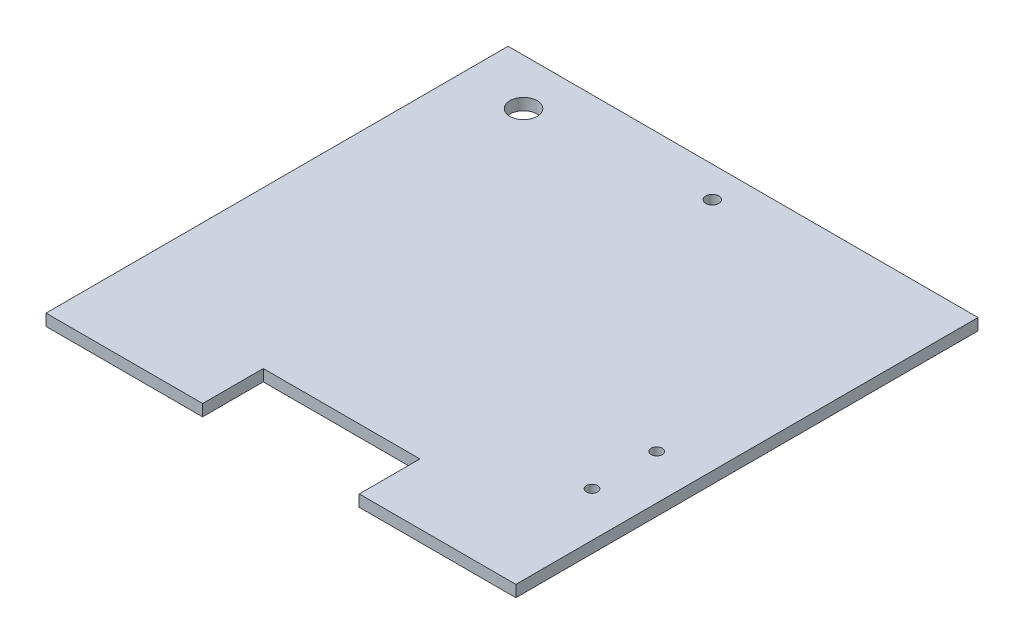
SolidWorks part; units mm, degrees
ref_plane "Front Plane" through (0, 0, 0) normal (0, 0, 1) x (1, 0, 0)
ref_plane "Top Plane" through (0, 0, 0) normal (0, 1, 0) x (1, 0, 0)
ref_plane "Right Plane" through (0, 0, 0) normal (1, 0, 0) x (0, 0, -1)
sketch "Sketch1" plane through (0, 0, 0) normal (0, 1, 0) x (1, 0, 0)
  line L1 (-96.84, -95.25) -> (96.84, -95.25)
  line L2 (-96.84, -95.25) -> (-96.84, 95.25)
  line L3 (-96.84, 95.25) -> (96.84, 95.25)
  line L4 (96.84, -95.25) -> (96.84, 95.25)
  line L5 (-96.84, -95.25) -> (96.84, 95.25) construction
  line L6 (-96.84, 95.25) -> (96.84, -95.25) construction
  point P0 (0, 0)
  dimension "D1" = 193.68
  dimension "D2" = 190.5
extrude "Boss-Extrude1" add sketch "Sketch1" along normal blind 4.78
sketch "Sketch2" plane through (0, 4.78, 0) normal (0, 1, 0) x (1, 0, 0)
  line L0 (96.84, 95.25) -> (-96.84, 95.25) construction
  line L1 (96.84, -95.25) -> (96.84, 95.25) construction
  circle A0 centre (0, 82.55) radius 2.6797
  point P4 (0, 95.25)
  dimension "D1" = 5.3594
  dimension "D2" = 12.7
  dimension "D3" = 96.84
extrude "Cut-Extrude1" cut sketch "Sketch2" against normal through all
sketch "Sketch3" plane through (0, 4.78, 0) normal (0, 1, 0) x (1, 0, 0)
  line L0 (0, -95.25) -> (-32.28, -95.25)
  line L1 (-96.84, -95.25) -> (96.84, -95.25) construction
  line L2 (-32.28, -95.25) -> (-32.28, -70.25)
  line L3 (-32.28, -70.25) -> (32.28, -70.25)
  line L4 (32.28, -70.25) -> (32.28, -95.25)
  line L5 (32.28, -95.25) -> (0, -95.25)
  line L6 (96.84, -95.25) -> (96.84, 95.25) construction
  dimension "D1" = 64.56
  dimension "D2" = 64.56
  dimension "D3" = 25
extrude "Cut-Extrude2" cut sketch "Sketch3" against normal through all
sketch "Sketch5" plane through (0, 4.78, 0) normal (0, 1, 0) x (1, 0, 0)
  line L4 (42.484, -0.2032) -> (87.95, -0.2032)
  line L5 (87.95, -0.2032) -> (87.95, -63.5)
  line L6 (87.95, -63.5) -> (42.484, -63.5)
  line L7 (42.484, -63.5) -> (42.484, -0.2032)
  line L8 (96.84, -95.25) -> (96.84, 95.25) construction
  line L9 (32.28, -95.25) -> (96.84, -95.25) construction
  line L10 (96.84, 95.25) -> (-96.84, 95.25) construction
  line L15 (-96.84, 95.25) -> (-96.84, -95.25) construction
  circle A2 centre (78.425, -18.771) radius 2.286
  circle A3 centre (78.425, -45.441) radius 2.286
  circle A4 centre (-71.44, 76.2) radius 5.6134
  dimension "D3" = 31.75
  dimension "D5" = 25.4
  dimension "D10" = 4.572
  dimension "D11" = 18.059
  dimension "D12" = 26.67
  dimension "D13" = 18.5678
  dimension "D14" = 9.525
  dimension "D4" = 19.05
  dimension "D2" = 8.89
  dimension "D8" = 45.466
  dimension "D9" = 63.2968
extrude "Cut-Extrude3" cut sketch "Sketch5" against normal through all contours A2 | A4 | A3
